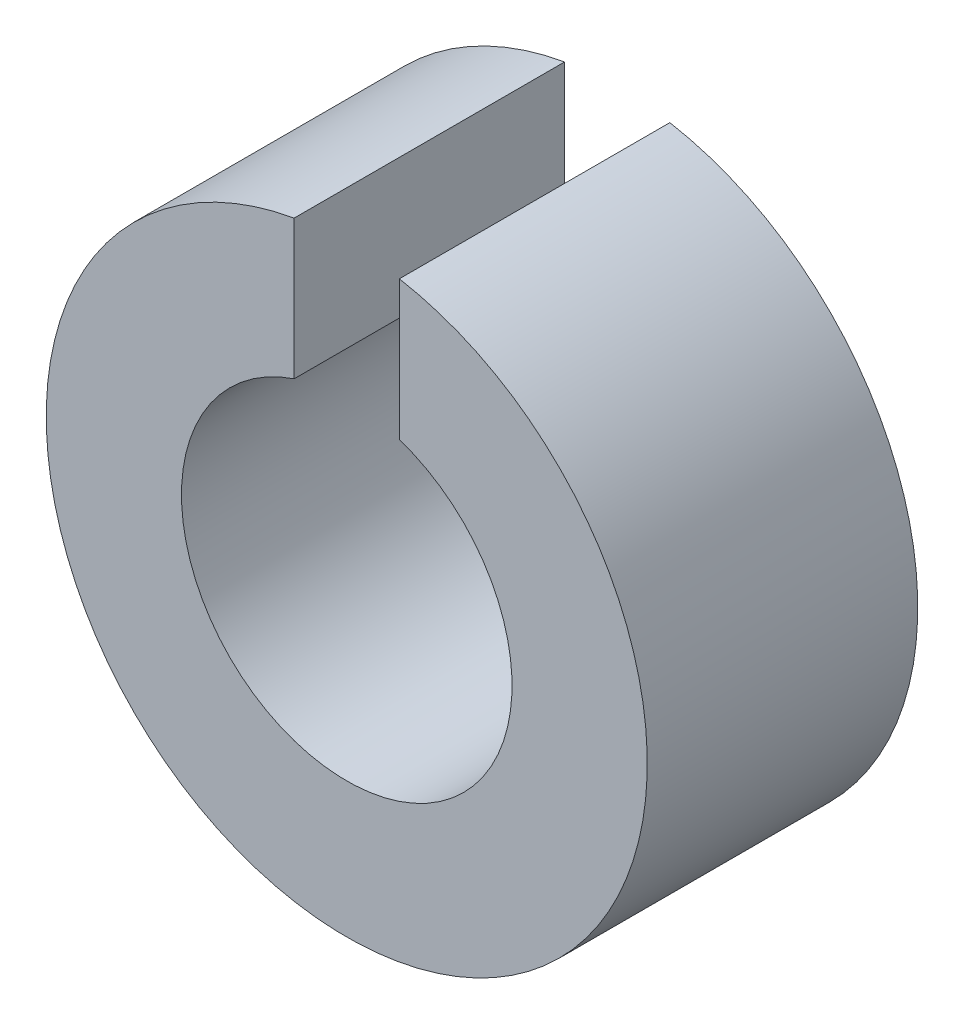
SolidWorks part; units mm, degrees
material "Тефлон"
ref_plane "Спереди" through (0, 0, 0) normal (0, 0, 1) x (1, 0, 0)
ref_plane "Сверху" through (0, 0, 0) normal (0, 1, 0) x (1, 0, 0)
ref_plane "Справа" through (0, 0, 0) normal (1, 0, 0) x (0, 0, -1)
sketch "Эскиз1" plane through (0, 0, 0) normal (0, 0, 1) x (1, 0, 0)
  circle A0 centre (0, 0) radius 10
  circle A1 centre (0, 0) radius 5.5
  dimension "D1" = 20
  dimension "D2" = 11
extrude "Бобышка-Вытянуть1" add sketch "Эскиз1" along normal blind 9
sketch "Эскиз2" plane through (0, 0, 9) normal (0, 0, 1) x (1, 0, 0)
  line L1 (-1.75, 17.5) -> (1.75, 17.5)
  line L2 (-1.75, 17.5) -> (-1.75, 2.5)
  line L3 (-1.75, 2.5) -> (1.75, 2.5)
  line L4 (1.75, 17.5) -> (1.75, 2.5)
  line L5 (-1.75, 17.5) -> (1.75, 2.5) construction
  line L6 (-1.75, 2.5) -> (1.75, 17.5) construction
  circle A0 centre (0, 0) radius 10 construction
  point P0 (0, 10)
  dimension "D1" = 3.5
  dimension "D2" = 15
extrude "Вырез-Вытянуть1" cut sketch "Эскиз2" against normal through all
